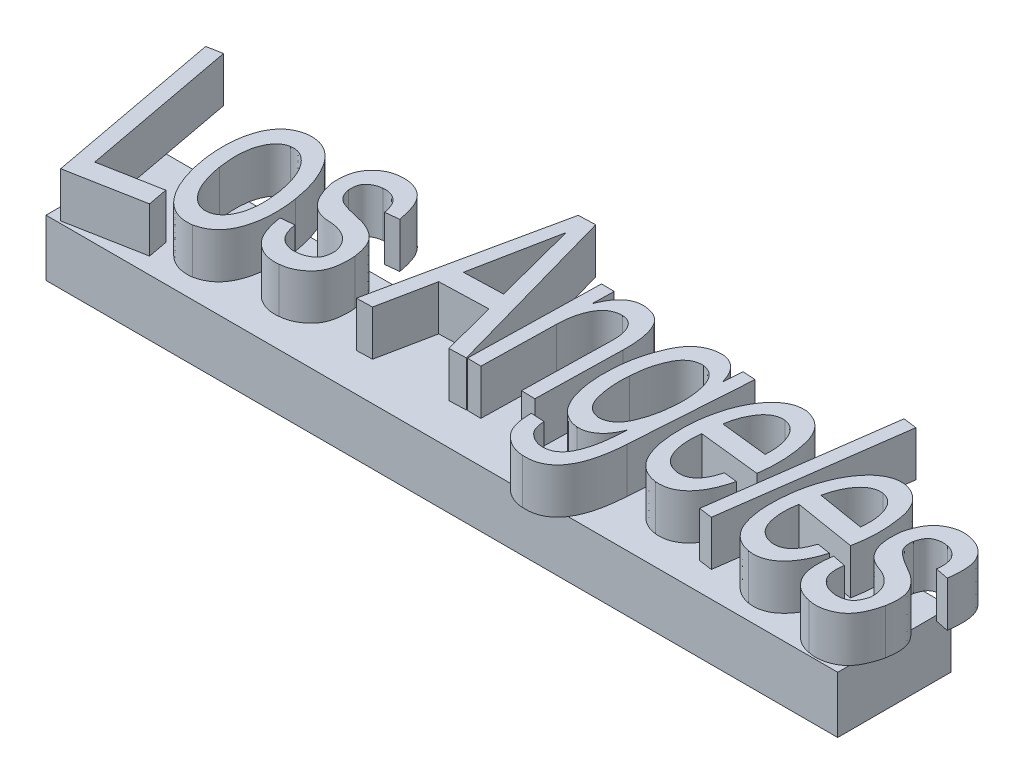
SolidWorks part; units mm, degrees
ref_plane "Front Plane" through (0, 0, 0) normal (0, 0, 1) x (1, 0, 0)
ref_plane "Top Plane" through (0, 0, 0) normal (0, 1, 0) x (1, 0, 0)
ref_plane "Right Plane" through (0, 0, 0) normal (1, 0, 0) x (0, 0, -1)
sketch "Sketch1" plane through (0, 0, 0) normal (0, 1, 0) x (1, 0, 0)
  line L1 (0, 0) -> (88.9, 0)
  line L2 (0, 0) -> (0, 12.7)
  line L3 (0, 12.7) -> (88.9, 12.7)
  line L4 (88.9, 0) -> (88.9, 12.7)
  dimension "D1" = 12.7
  dimension "D2" = 88.9
extrude "Boss-Extrude1" add sketch "Sketch1" along normal blind 6.35
sketch "Sketch4" plane through (0, 6.35, 0) normal (0, 1, 0) x (1, 0, 0)
  line L0 (44.45, 0) -> (44.45, 6.2795) construction
  line L1 (0, 0) -> (88.9, 0) construction
  spline S0 degree 2 poles (0, 0) (44.45, 9.4469) (88.9, 0) knots 0 0 0 1 1 1 construction
  text T0 "<b>Los Angeles</b>" font "HelveticaNeueLT Pro 55 Roman" height 20.32
extrude "Boss-Extrude2" add sketch "Sketch4" along normal blind 5.08
